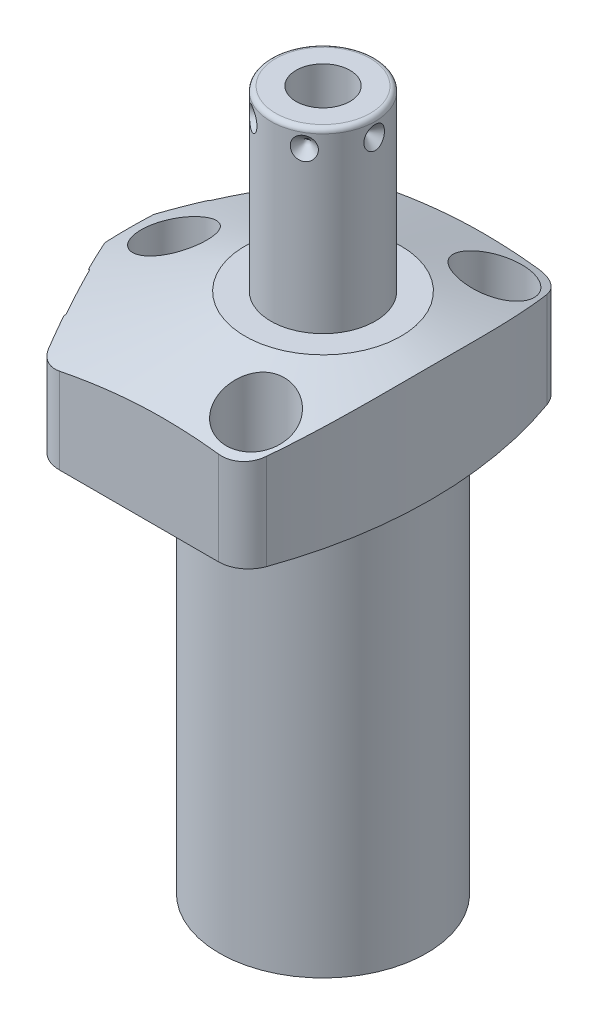
SolidWorks part; units mm, degrees
material "Alloy Steel"
ref_plane "Front Plane" through (0, 0, 0) normal (0, 0, 1) x (1, 0, 0)
ref_plane "Top Plane" through (0, 0, 0) normal (0, 1, 0) x (1, 0, 0)
ref_plane "Right Plane" through (0, 0, 0) normal (1, 0, 0) x (0, 0, -1)
ref_plane "Plane1" through (0, 0, 0) normal (0, 0, 1) x (0, -1, 0)
sketch "Sketch1" plane through (0, 0, 0) normal (0, 0, 1) x (0, -1, 0)
  line L0 (0, 44.45) -> (-26.9748, 44.45)
  line L1 (-26.9748, 44.45) -> (-26.9748, 0)
  line L2 (-26.9748, 0) -> (84.1502, 0)
  line L3 (84.1502, 0) -> (84.1502, 22.098)
  line L4 (84.1502, 22.098) -> (0, 22.098)
  line L5 (0, 22.098) -> (0, 44.45)
  line L6 (-32.531, 0) -> (89.7065, 0) construction
  dimension "D1" = 111.125
  dimension "D2" = 26.9748
  dimension "D3" = 88.9
  dimension "D4" = 44.196
revolve "Revolve1" add sketch "Sketch1" angle 360 about L6
ref_plane "Plane2" through (0, 0, 0) normal (0, -1, 0) x (0, 0, -1)
sketch "Sketch2" plane through (0, 0, 0) normal (0, -1, 0) x (0, 0, -1)
  line L0 (34.1122, -28.4984) -> (34.1122, 28.4984)
  line L2 (-34.1122, 28.4984) -> (-34.1122, -28.4984)
  line L3 (0, -32.1458) -> (0, 48.0974) construction
  arc A0 (34.1122, -28.4984) -> (34.1122, 28.4984) centre (0, 0) ccw
  circle A1 centre (0, 0) radius 44.45
  arc A2 (-34.1122, 28.4984) -> (-34.1122, -28.4984) centre (0, 0) ccw
  point P4 (0, 0)
  dimension "D1" = 68.2244
  dimension "D2" = 0
extrude "Cut-Extrude1" cut sketch "Sketch2" against normal up to next
ref_plane "Plane3" through (0, 0, 0) normal (0, -1, 0) x (-1, 0, 0)
sketch "Sketch3" plane through (0, 0, 0) normal (0, -1, 0) x (-1, 0, 0)
  line L0 (25.9049, 34.1122) -> (44.0427, 0)
  line L1 (44.0427, 0) -> (25.9049, -34.1122)
  line L2 (-39.4859, -20.995) -> (73.8214, 39.2515) construction
  line L3 (0, 0) -> (44.0427, 0) construction
  line L6 (-28.4984, -34.1122) -> (28.4984, -34.1122)
  line L7 (28.4984, 34.1122) -> (-28.4984, 34.1122)
  line L8 (25.9049, -34.1122) -> (28.4984, -34.1122)
  line L9 (28.4984, 34.1122) -> (25.9049, 34.1122)
  arc A2 (-28.4984, 34.1122) -> (-28.4984, -34.1122) centre (0, 0) ccw
  arc A3 (28.4984, -34.1122) -> (28.4984, 34.1122) centre (0, 0) ccw
  arc A5 (28.4984, -34.1122) -> (28.4984, 34.1122) centre (0, 0) ccw
  dimension "D1" = 28
  dimension "D2" = 38.8874
  dimension "D3" = 0
extrude "Cut-Extrude2" cut sketch "Sketch3" against normal up to next
ref_plane "Plane4" through (0, 0, 0) normal (0, -1, 0) x (-1, 0, 0)
sketch "S2D0002" plane through (0, 0, 0) normal (0, -1, 0) x (-1, 0, 0)
  line L0 (41.275, 85.425) -> (41.275, -85.425)
  arc A0 (41.275, 85.425) -> (41.275, -85.425) centre (65.8876, 0) ccw
  dimension "D3" = 88.9
  dimension "D1" = 65.8876
  dimension "D2" = 41.275
extrude "Cut-Extrude3" cut sketch "S2D0002" against normal blind 38.0873 flip side to cut
fillet "Fillet1" radius 6.35 2 edges at (16.2073, 13.4874, 34.1122) (16.2073, 13.4874, -34.1122)
fillet "Fillet2" radius 6.35 1 edges at (-25.9049, 13.4874, 34.1122)
fillet "Fillet3" radius 6.35 1 edges at (-25.9049, 13.4874, -34.1122)
ref_plane "Plane5" through (0, 0, 0) normal (0, 0, 1) x (1, 0, 0)
sketch "Sketch5" plane through (0, 0, 0) normal (0, 0, 1) x (1, 0, 0)
  line L0 (-16.637, 26.9748) -> (-47.625, 15.6961)
  line L1 (0, 7.6649) -> (0, 27.5963) construction
  line L3 (11.854, 26.9748) -> (-22.0895, 26.9748) construction
  line L4 (-16.637, 26.9748) -> (-47.625, 26.9748)
  line L5 (-47.625, 26.9748) -> (-47.625, 15.6961)
  dimension "D1" = 33.274
  dimension "D2" = 20
  dimension "D3" = 47.625
revolve "Cut-Revolve1" cut sketch "Sketch5" angle 360 about L1
ref_plane "Plane6" through (-34.1113, 10.287, -18.1373) normal (0, 1, 0) x (0.4695, 0, -0.8829)
sketch "Sketch6" plane through (-34.1113, 10.287, -18.1373) normal (0, 1, 0) x (0.4695, 0, -0.8829)
  line L0 (0, 0) -> (6.1849, 0)
  line L1 (6.1849, 0) -> (5.6423, -2.5527)
  line L2 (5.6423, -2.5527) -> (4.9784, -3.2166)
  line L3 (4.9784, -3.2166) -> (4.9784, -15.748)
  line L4 (4.9784, -15.748) -> (0, -15.748)
  line L5 (0, -15.748) -> (0, 0)
  line L6 (0, -16.5354) -> (0, 0.7874) construction
  dimension "D1" = 15.748
revolve "Cut-Revolve2" cut sketch "Sketch6" angle 360 about L6
ref_plane "Plane7" through (-34.1113, 10.287, 18.1373) normal (0, 1, 0) x (-0.4695, 0, -0.8829)
sketch "Sketch7" plane through (-34.1113, 10.287, 18.1373) normal (0, 1, 0) x (-0.4695, 0, -0.8829)
  line L0 (0, 0) -> (6.1849, 0)
  line L1 (6.1849, 0) -> (5.6423, -2.5527)
  line L2 (5.6423, -2.5527) -> (4.9784, -3.2166)
  line L3 (4.9784, -3.2166) -> (4.9784, -15.748)
  line L4 (4.9784, -15.748) -> (0, -15.748)
  line L5 (0, -15.748) -> (0, 0)
  line L6 (0, -16.5354) -> (0, 0.7874) construction
  dimension "D1" = 15.748
revolve "Cut-Revolve3" cut sketch "Sketch7" angle 360 about L6
ref_plane "Plane8" through (-13.4874, 2.667, -26.5938) normal (0, 0, 1) x (-1, 0, 0)
sketch "Sketch8" plane through (-13.4874, 2.667, -26.5938) normal (0, 0, 1) x (-1, 0, 0)
  line L0 (0, 0) -> (4.5466, 0)
  line L1 (4.5466, 0) -> (4.1066, -2.0701)
  line L2 (4.1066, -2.0701) -> (3.4544, -2.7223)
  line L3 (3.4544, -2.7223) -> (3.4544, -12.573)
  line L4 (3.4544, -12.573) -> (0, -12.573)
  line L5 (0, -12.573) -> (0, 0)
  line L6 (0, -13.2017) -> (0, 0.6287) construction
  dimension "D1" = 12.573
revolve "Cut-Revolve4" cut sketch "Sketch8" angle 360 about L6
ref_plane "Plane9" through (-13.4874, 2.667, 26.5938) normal (0, 0, 1) x (-1, 0, 0)
sketch "Sketch9" plane through (-13.4874, 2.667, 26.5938) normal (0, 0, 1) x (-1, 0, 0)
  line L0 (0, 0) -> (4.5466, 0)
  line L1 (4.5466, 0) -> (4.1066, -2.0701)
  line L2 (4.1066, -2.0701) -> (3.4544, -2.7223)
  line L3 (3.4544, -2.7223) -> (3.4544, -12.573)
  line L4 (3.4544, -12.573) -> (0, -12.573)
  line L5 (0, -12.573) -> (0, 0)
  line L6 (0, -13.2017) -> (0, 0.6287) construction
  dimension "D1" = 12.573
revolve "Cut-Revolve5" cut sketch "Sketch9" angle 360 about L6
sketch "Sketch17" plane through (-34.3355, 0, 18.2565) normal (-0.8829, 0, 0.4695) x (0.4695, 0, 0.8829)
  circle A0 centre (0, 10.287) radius 10.4775
  dimension "D1" = 20.955
extrude "Cut-Extrude4" cut sketch "Sketch17" against normal blind 0.254
sketch "Sketch18" plane through (0, 0, 0) normal (0, -1, 0) x (1, 0, 0)
  circle A0 centre (-13.4874, 26.5938) radius 5.5626
  dimension "D1" = 11.1252
extrude "Cut-Extrude5" cut sketch "Sketch18" against normal blind 2.667
mirror "Mirror1" about plane through (0, 0, 0) normal (0, 0, 1) of "Cut-Extrude5", "Cut-Extrude4"
ref_plane "Plane10" through (0, 0, 0) normal (1, 0, 0) x (0, 0, -1)
sketch "Sketch10" plane through (0, 0, 0) normal (1, 0, 0) x (0, 0, -1)
  line L0 (0, 26.9748) -> (-11.1125, 26.9748)
  line L1 (-11.1125, 26.9748) -> (-11.1125, 63.8302)
  line L2 (-10.0965, 64.8462) -> (0, 64.8462)
  line L3 (0, 64.8462) -> (0, 26.9748)
  line L4 (0, 14.3517) -> (0, 66.7398) construction
  line L5 (16.637, 26.9748) -> (-16.637, 26.9748) construction
  line L6 (-29.8978, 0) -> (29.8978, 0) construction
  arc A0 (-10.0965, 64.8462) -> (-11.1125, 63.8302) centre (-10.0965, 63.8302) ccw
  dimension "D2" = 1.016
  dimension "D1" = 64.8462
  dimension "D3" = 22.225
revolve "Revolve2" add sketch "Sketch10" angle 360 about L4
ref_plane "Plane11" through (5.7531, 64.8462, 0) normal (0, 0, 1) x (1, 0, 0)
sketch "S2D0001" plane through (5.7531, 64.8462, 0) normal (0, 0, 1) x (1, 0, 0)
  line L0 (0, 0) -> (0, -17.018)
  line L1 (0, -17.018) -> (-5.7531, -20.4748)
  line L2 (0, 0) -> (-5.7531, 0)
  line L3 (-5.7531, 0) -> (-5.7531, -20.4748)
  line L4 (-5.7531, -27.7363) -> (-5.7531, 1.0237) construction
  line L5 (4.3434, 0) -> (-15.8496, 0) construction
  dimension "D1" = 11.5062
  dimension "D2" = 17.018
  dimension "D3" = 59
revolve "Cut-Revolve6" cut sketch "S2D0001" angle 360 about L4
ref_plane "Plane13" through (-13.4874, 0, 26.5938) normal (1, 0, 0) x (0, 0, -1)
sketch "Sketch14" plane through (-13.4874, 0, 26.5938) normal (1, 0, 0) x (0, 0, -1)
  line L0 (5.461, 2.667) -> (5.461, 0.9398)
  line L1 (5.461, 0.9398) -> (5.3016, 0.9398)
  line L2 (2.667, 0.4318) -> (2.667, 0.127)
  line L3 (2.667, 0.127) -> (1.5875, 0.127)
  line L4 (1.5875, 0.127) -> (1.5875, 10.6172)
  line L5 (1.5875, 10.6172) -> (3.2512, 10.6172)
  line L6 (3.2512, 10.6172) -> (3.2512, 2.667)
  line L7 (3.2512, 2.667) -> (5.461, 2.667)
  line L8 (3.175, 0.9398) -> (3.8424, 0.9398)
  line L9 (0, -1.0109) -> (0, 11.1709) construction
  arc A0 (3.175, 0.9398) -> (2.667, 0.4318) centre (3.175, 0.4318) ccw
  arc A1 (3.8424, 0.9398) -> (5.3016, 0.9398) centre (4.572, 0.4318) ccw
  dimension "D1" = 2.54
  dimension "D2" = 7.9502
revolve "Revolve3" add sketch "Sketch14" angle 360 about L9
ref_plane "Plane14" through (-11.1125, 60.8838, 0) normal (0, 0, 1) x (0, 1, 0)
sketch "Sketch15" plane through (-11.1125, 60.8838, 0) normal (0, 0, 1) x (0, 1, 0)
  line L0 (0, 0) -> (2.413, 0)
  line L1 (2.413, 0) -> (0, -2.413)
  line L2 (0, 0) -> (0, -2.413)
  line L3 (0, -5.1094) -> (0, 0.1207) construction
  line L4 (2.9464, 0) -> (-33.909, 0) construction
  line L5 (3.9624, -21.209) -> (3.9624, -1.016) construction
  dimension "D1" = 3.9624
  dimension "D2" = 4.826
  dimension "D3" = 45
revolve "Cut-Revolve7" cut sketch "Sketch15" angle 360 about L3
pattern_circular "CirPattern1" count 6 over 360 about axis through (0, 14.3517, 0) along (0, -1, 0) of "Cut-Revolve7"
hole_wizard "Hole1" positions "Sketch20" profile "Sketch19" legacy end condition up to next
sketch "Sketch20" plane through (0, 26.9748, 0) normal (0, 1, 0) x (-1, 0, 0)
  line L0 (0, 0) -> (47.6205, 0) construction
  line L1 (0, 0) -> (0, 38.9977) construction
  point P0 (-11.1252, -25.4)
  point P10 (31.75, 0)
  point P14 (-11.1252, 25.4)
  dimension "D1" = 11.1252
  dimension "D2" = 25.4
  dimension "D3" = 31.75
sketch "Sketch19" plane through (11.1252, 26.9748, -25.4) normal (1, 0, 0) x (0, 0, 1)
  line L0 (0, 0) -> (0, 26.9748)
  line L1 (0, 26.9748) -> (4.3688, 26.9748)
  line L2 (4.3688, 26.9748) -> (4.3688, 16.6624)
  line L3 (4.3688, 16.6624) -> (6.9977, 16.6624)
  line L4 (6.9977, 16.6624) -> (6.9977, 0)
  line L5 (6.9977, 0) -> (0, 0)
  line L6 (0, 110) -> (0, -10) construction
  dimension "Diameter" = 8.7376
  dimension "Depth" = 26.9748
  dimension "C-Bore Diameter" = 13.9954
  dimension "C-Bore Depth" = 16.6624
mirror "Mirror2" about plane through (0, 0, 0) normal (0, 0, 1) of "Revolve3"
